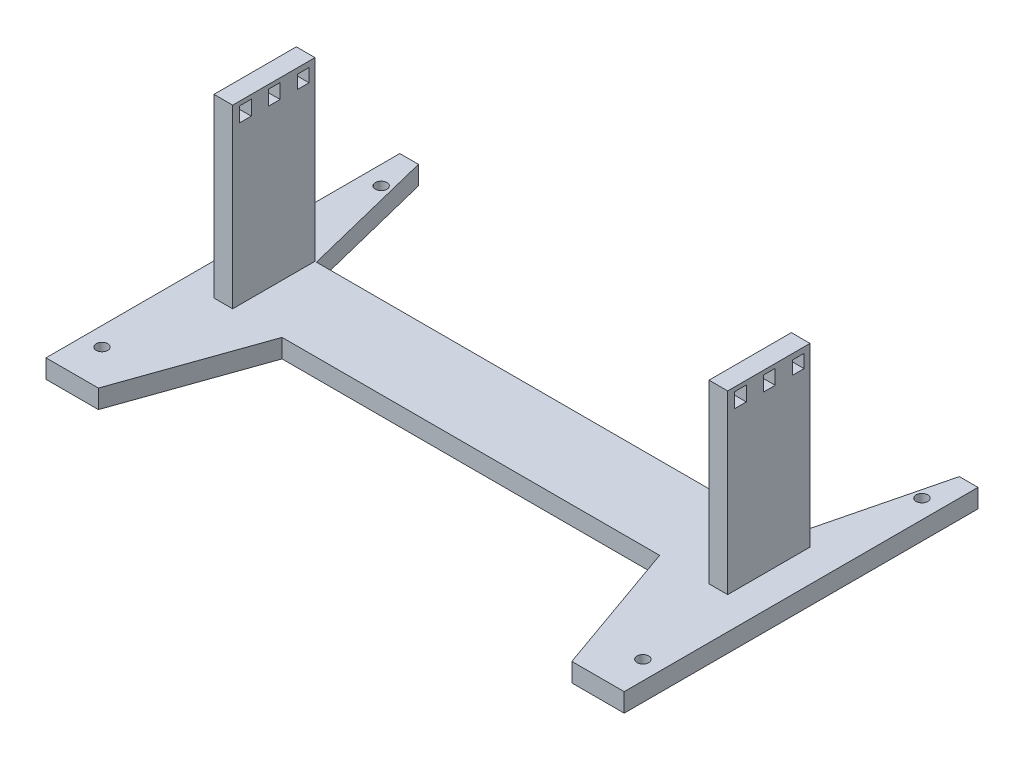
SolidWorks part; units mm, degrees
ref_plane "Front" through (0, 0, 0) normal (0, 0, 1) x (1, 0, 0)
ref_plane "Top" through (0, 0, 0) normal (0, 1, 0) x (1, 0, 0)
ref_plane "Right" through (0, 0, 0) normal (1, 0, 0) x (0, 0, -1)
sketch "草图1" plane through (0, 0, 0) normal (0, 1, 0) x (1, 0, 0)
  line L0 (0, 0) -> (20, 0) construction
  line L1 (20, 0) -> (129, 0) construction
  line L2 (0, 0) -> (0, 43.8486) construction
  line L3 (-129, 0) -> (-178, 0) construction
  circle A7 centre (0, 0) radius 178
  point P33 (0, 0)
sketch "草图2" plane through (0, 3, 0) normal (0, 1, 0) x (1, 0, 0)
  line L0 (0, 0) -> (-125.865, -125.865) construction
  line L1 (125.865, 125.865) -> (115.2584, 115.2584) construction
  line L2 (-125.865, -125.865) -> (-95.8738, -95.8738) construction
  line L3 (-95.8738, -95.8738) -> (-90.2169, -101.5306) construction
  line L5 (-90.2169, -101.5306) -> (-95.1667, -106.4804) construction
  line L6 (-95.1667, -106.4804) -> (-90.2169, -111.4301) construction
  line L7 (-90.2169, -111.4301) -> (-85.2672, -106.4804) construction
  line L8 (-85.2672, -106.4804) -> (-90.2169, -101.5306) construction
  line L9 (-90.2169, -101.5306) -> (-90.2169, -111.4301) construction
  line L20 (-90.2169, -111.4301) -> (-90.2169, -106.4804) construction
  line L21 (-90.2169, -106.4804) -> (-85.2672, -106.4804) construction
  line L29 (0, 0) -> (-125.865, 125.865) construction
  line L38 (0, 0) -> (125.865, 125.865) construction
  line L47 (0, 0) -> (125.865, -125.865) construction
  circle A6 centre (0, 0) radius 178 construction
  circle A7 centre (115.2584, 115.2584) radius 10.414
  circle A9 centre (-90.2169, -106.4804) radius 5.2
  circle A10 centre (-106.4804, -90.2169) radius 5.2
  circle A11 centre (115.2584, -115.2584) radius 10.414
  circle A12 centre (-115.2584, -115.2584) radius 10.414
  circle A13 centre (-115.2584, 115.2584) radius 10.414
  circle A14 centre (-90.2169, 106.4804) radius 5.2
  circle A15 centre (-106.4804, 90.2169) radius 5.2
  circle A16 centre (106.4804, 90.2169) radius 5.2
  circle A17 centre (90.2169, 106.4804) radius 5.2
  circle A18 centre (90.2169, -106.4804) radius 5.2
  circle A19 centre (106.4804, -90.2169) radius 5.2
  point P27 (0, 0)
  point P43 (0, 0)
  dimension "D1" = 4
  dimension "D2" = 4
sketch "草图4" plane through (0, 0, 0) normal (0, -1, 0) x (1, 0, 0)
  circle A1 centre (80.5, 0) radius 54.5
  circle A3 centre (-80.5, 0) radius 54.5
  point P3 (0, 0)
  point P4 (0, 0)
sketch "草图5" plane through (0, 3, 0) normal (0, 1, 0) x (1, 0, 0)
  line L0 (-26, 0) -> (0, 0) construction
  line L1 (26, 0) -> (26, 17.325) construction
  line L2 (0.6, 17.325) -> (3.775, 17.325) construction
  line L3 (0.6, 17.325) -> (0.6, -30.725) construction
  line L4 (0.6, -30.725) -> (3.775, -30.725) construction
  line L5 (3.775, -30.725) -> (3.775, -27.55) construction
  line L6 (3.775, 17.325) -> (3.775, 14.15) construction
  line L7 (26, 17.325) -> (22.825, 17.325) construction
  line L8 (22.825, 17.325) -> (22.825, 14.15) construction
  line L9 (26, 0) -> (26, -30.725) construction
  line L10 (26, -30.725) -> (22.825, -30.725) construction
  line L11 (22.825, -30.725) -> (22.825, -27.55) construction
  line L12 (-26, 0) -> (-26, -17.325) construction
  line L13 (-26, -17.325) -> (-22.825, -17.325) construction
  line L14 (-0.6, -17.325) -> (-0.6, 30.725) construction
  line L15 (-0.6, 30.725) -> (-3.775, 30.725) construction
  line L16 (-3.775, 30.725) -> (-3.775, 27.55) construction
  line L17 (-22.825, -17.325) -> (-22.825, -14.15) construction
  line L18 (-0.6, -17.325) -> (-3.775, -17.325) construction
  line L19 (-3.775, -17.325) -> (-3.775, -14.15) construction
  line L20 (-26, 0) -> (-26, 30.725) construction
  line L21 (-26, 30.725) -> (-22.825, 30.725) construction
  line L22 (-22.825, 30.725) -> (-22.825, 27.55) construction
  line L23 (0, 0) -> (26, 0) construction
  line L24 (80.5, 80.5) -> (80.5, 54.5) construction
  line L25 (161, 0) -> (135, 0) construction
  line L26 (80.5, -80.5) -> (80.5, -54.5) construction
  line L27 (-80.5, -54.5) -> (-97.825, -54.5) construction
  line L28 (-80.5, -54.5) -> (-80.5, -80.5) construction
  line L29 (-135, 0) -> (-135, 17.325) construction
  line L30 (-135, 0) -> (-161, 0) construction
  line L31 (-80.5, 54.5) -> (-63.175, 54.5) construction
  line L32 (-80.5, 54.5) -> (-80.5, 80.5) construction
  circle A0 centre (-94.65, -57.675) radius 1.829
  circle A29 centre (-94.65, -76.725) radius 1.829
  circle A50 centre (-22.825, 27.55) radius 1.829
  circle A51 centre (-3.775, 27.55) radius 1.829
  circle A52 centre (-22.825, -14.15) radius 1.829
  circle A53 centre (-3.775, -14.15) radius 1.829
  circle A54 centre (3.775, 14.15) radius 1.829
  circle A55 centre (22.825, 14.15) radius 1.829
  circle A56 centre (3.775, -27.55) radius 1.829
  circle A57 centre (22.825, -27.55) radius 1.829
  circle A58 centre (94.65, 76.725) radius 1.829
  circle A59 centre (94.65, 57.675) radius 1.829
  circle A60 centre (52.95, 57.675) radius 1.829
  circle A61 centre (52.95, 76.725) radius 1.829
  circle A62 centre (157.225, -14.15) radius 1.829
  circle A63 centre (138.175, -14.15) radius 1.829
  circle A64 centre (138.175, 27.55) radius 1.829
  circle A65 centre (157.225, 27.55) radius 1.829
  circle A66 centre (66.35, -76.725) radius 1.829
  circle A67 centre (66.35, -57.675) radius 1.829
  circle A68 centre (108.05, -57.675) radius 1.829
  circle A69 centre (108.05, -76.725) radius 1.829
  circle A70 centre (-52.95, -57.675) radius 1.829
  circle A71 centre (-52.95, -76.725) radius 1.829
  circle A72 centre (-138.175, 14.15) radius 1.829
  circle A73 centre (-157.225, 14.15) radius 1.829
  circle A74 centre (-138.175, -27.55) radius 1.829
  circle A75 centre (-157.225, -27.55) radius 1.829
  circle A76 centre (-66.35, 57.675) radius 1.829
  circle A77 centre (-66.35, 76.725) radius 1.829
  circle A78 centre (-108.05, 57.675) radius 1.829
  circle A79 centre (-108.05, 76.725) radius 1.829
  point P3 (0, 0)
  point P61 (94.5, 0)
  point P71 (80.5, 0)
  point P104 (-80.5, 0)
  point P115 (-94.5, 0)
  dimension "D1" = 4
  dimension "D2" = 4
sketch "草图6" plane through (0, 3, 0) normal (0, 1, 0) x (1, 0, 0)
  line L0 (115.2584, -115.2584) -> (91.9664, -115.2584) construction
  line L1 (91.9664, -115.2584) -> (91.9664, -80.5) construction
  line L2 (91.9664, -80.5) -> (80.5, -80.5) construction
  line L3 (80.5, -80.5) -> (80.5, -115.2584) construction
  line L4 (80.5, -115.2584) -> (81, -115.2584) construction
  line L5 (115.2584, -115.2584) -> (115.2584, -135.6448) construction
  line L6 (115.2584, -135.6448) -> (98.3164, -135.6448) construction
  line L7 (98.3164, 0) -> (98.3164, 150) construction
  line L8 (98.3164, 150) -> (0, 150) construction
  line L9 (0, 150) -> (0, 0) construction
  line L10 (91.9664, 0) -> (91.9664, 12.7) construction
  line L11 (80.5, 0) -> (80.5, 74.16) construction
  line L13 (80.5, 74.16) -> (64.1977, 74.16) construction
  line L14 (64.1977, 74.16) -> (64.1977, 46.16) construction
  line L15 (64.1977, 46.16) -> (80.5, 46.16) construction
  line L16 (0, 0) -> (53.1099, 0) construction
  line L17 (64.1977, 60.16) -> (0, 60.16) construction
  line L18 (91.9664, 120.32) -> (91.9664, 107.62) construction
  line L19 (98.3164, 0) -> (91.9664, 0)
  line L20 (91.9664, 0) -> (80.5, 0)
  line L21 (80.5, 0) -> (64.1977, 46.16)
  line L22 (64.1977, 46.16) -> (-64.1977, 46.16)
  line L23 (64.1977, 74.16) -> (80.5, 74.16)
  line L24 (80.5, 74.16) -> (91.9664, 120.32)
  line L25 (91.9664, 120.32) -> (98.3164, 120.32)
  line L26 (98.3164, 120.32) -> (98.3164, 0)
  line L27 (64.1977, 74.16) -> (-64.1977, 74.16)
  line L28 (-64.1977, 74.16) -> (-80.5, 74.16)
  line L29 (-80.5, 74.16) -> (-91.9664, 120.32)
  line L30 (-91.9664, 120.32) -> (-98.3164, 120.32)
  line L31 (-98.3164, 120.32) -> (-98.3164, 0)
  line L32 (-98.3164, 0) -> (-91.9664, 0)
  line L33 (-91.9664, 0) -> (-80.5, 0)
  line L34 (-80.5, 0) -> (-64.1977, 46.16)
  circle A1 centre (0, 0) radius 178 construction
  circle A2 centre (91.9664, 12.7) radius 1.984
  circle A3 centre (91.9664, 107.62) radius 1.984
  circle A4 centre (-91.9664, 12.7) radius 1.984
  circle A5 centre (-91.9664, 107.62) radius 1.984
  point P40 (0, 74.16)
  point P47 (0, 46.16)
extrude "凸台-拉伸2" add sketch "草图6" along normal blind 6.35
sketch "草图7" plane through (0, 9.35, 0) normal (0, 1, 0) x (1, 0, 0)
  line L0 (80.5, 74.16) -> (81, 74.16) construction
  line L1 (81, 74.16) -> (81, 46.16) construction
  line L2 (81, 46.16) -> (87.35, 46.16) construction
  line L3 (81, 74.16) -> (87.35, 74.16) construction
  line L4 (87.35, 74.16) -> (87.35, 46.16) construction
  line L5 (0, 0) -> (0, 46.16) construction
  line L6 (-64.1977, 46.16) -> (64.1977, 46.16) construction
  line L7 (-80.5, 0) -> (0, 0) construction
  line L8 (0, 0) -> (80.5, 0) construction
  line L9 (81, 74.16) -> (87.35, 74.16)
  line L10 (87.35, 74.16) -> (87.35, 46.16)
  line L11 (87.35, 46.16) -> (81, 46.16)
  line L12 (81, 46.16) -> (81, 74.16)
  line L13 (-87.35, 46.16) -> (-81, 46.16)
  line L14 (-87.35, 74.16) -> (-87.35, 46.16)
  line L15 (-81, 74.16) -> (-87.35, 74.16)
  line L16 (-81, 46.16) -> (-81, 74.16)
extrude "凸台-拉伸3" add sketch "草图7" along normal blind 60
sketch "草图8" plane through (87.35, 0, 0) normal (1, 0, 0) x (0, 0, -1)
  line L0 (74.16, 69.35) -> (70.13, 69.35) construction
  line L1 (46.16, 69.35) -> (74.16, 69.35) construction
  line L2 (70.13, 69.35) -> (70.13, 65.44) construction
  line L3 (70.13, 65.44) -> (60.31, 65.44) construction
  line L4 (60.31, 65.44) -> (60.31, 69.35) construction
  line L5 (60.31, 69.35) -> (50.49, 69.35) construction
  line L6 (50.49, 69.35) -> (50.49, 65.44) construction
  line L7 (52.49, 65.44) -> (52.49, 62.94) construction
  line L8 (52.49, 62.94) -> (48.49, 62.94) construction
  line L9 (48.49, 62.94) -> (48.49, 65.44) construction
  line L10 (48.49, 65.44) -> (48.49, 67.94) construction
  line L11 (48.49, 67.94) -> (52.49, 67.94) construction
  line L12 (52.49, 67.94) -> (52.49, 65.44) construction
  line L13 (62.31, 65.44) -> (62.31, 62.94) construction
  line L14 (62.31, 62.94) -> (58.31, 62.94) construction
  line L15 (58.31, 62.94) -> (58.31, 65.44) construction
  line L16 (58.31, 65.44) -> (58.31, 67.94) construction
  line L17 (58.31, 67.94) -> (62.31, 67.94) construction
  line L18 (62.31, 67.94) -> (62.31, 65.44) construction
  line L19 (68.13, 65.44) -> (68.13, 62.94) construction
  line L20 (68.13, 62.94) -> (72.13, 62.94) construction
  line L21 (72.13, 62.94) -> (72.13, 67.44) construction
  line L22 (72.13, 67.44) -> (68.13, 67.44) construction
  line L23 (68.13, 67.44) -> (68.13, 65.44) construction
  line L24 (48.49, 67.94) -> (52.49, 67.94)
  line L25 (52.49, 67.94) -> (52.49, 62.94)
  line L26 (52.49, 62.94) -> (48.49, 62.94)
  line L27 (48.49, 62.94) -> (48.49, 67.94)
  line L28 (62.31, 67.94) -> (62.31, 62.94)
  line L29 (62.31, 62.94) -> (58.31, 62.94)
  line L30 (58.31, 62.94) -> (58.31, 67.94)
  line L31 (58.31, 67.94) -> (62.31, 67.94)
  line L32 (68.13, 67.44) -> (68.13, 62.94)
  line L33 (68.13, 62.94) -> (72.13, 62.94)
  line L34 (72.13, 62.94) -> (72.13, 67.44)
  line L35 (72.13, 67.44) -> (68.13, 67.44)
extrude "切除-拉伸3" cut sketch "草图8" against normal blind 250
